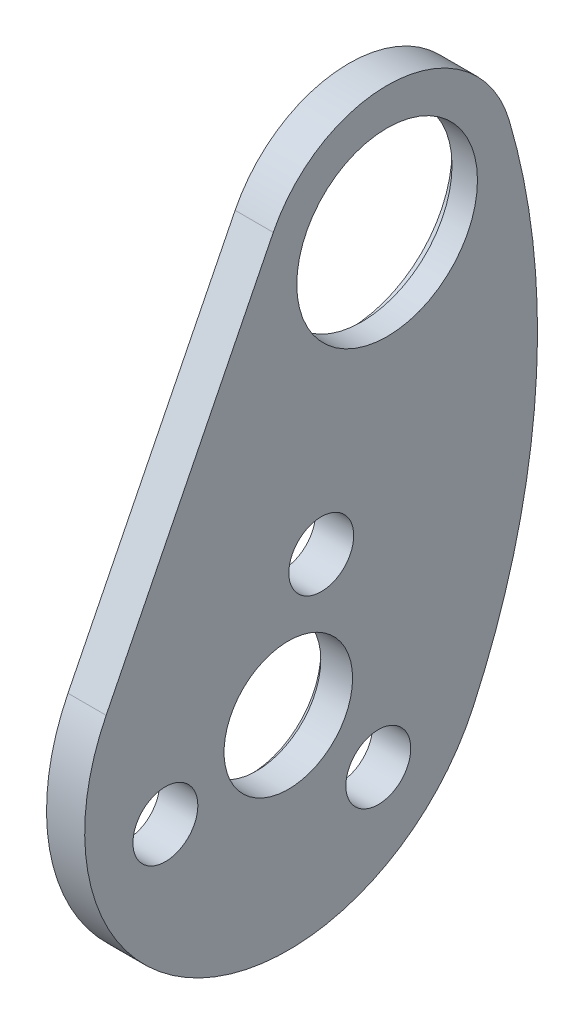
SolidWorks part; units mm, degrees
material "Thornel Mat VMA"
ref_plane "前视基准面" through (0, 0, 0) normal (0, 0, 1) x (1, 0, 0)
ref_plane "上视基准面" through (0, 0, 0) normal (0, 1, 0) x (1, 0, 0)
ref_plane "右视基准面" through (0, 0, 0) normal (1, 0, 0) x (0, 0, -1)
sketch "草图1" plane through (0, 0, 0) normal (1, 0, 0) x (0, 0, -1)
  line L0 (0, 0) -> (-7.7646, -28.9778) construction
  line L1 (-8.9465, 4.4678) -> (-22.0789, -21.8294)
  line L2 (-7.7646, -28.9778) -> (-17.2624, -28.9778) construction
  circle A0 centre (0, 0) radius 10
  circle A1 centre (-7.7646, -28.9778) radius 16
  arc A2 (6.7665, -35.6746) -> (9.5965, 2.8121) centre (-43.1841, -12.6543) ccw
  dimension "D1" = 32
  dimension "D2" = 20
  dimension "D4" = 55
  dimension "D3" = 30
  dimension "D5" = 105
extrude "凸台-拉伸1" add sketch "草图1" along normal blind 3
sketch "草图2" plane through (0, 0, 0) normal (-1, 0, 0) x (0, 0, 1)
  circle A0 centre (0, 0) radius 7.1
  arc A1 (8.9465, 4.4678) -> (-9.5965, 2.8121) centre (0, 0) ccw construction
  circle A2 centre (7.7646, -28.9778) radius 5.05
  arc A3 (-6.7665, -35.6746) -> (22.0789, -21.8294) centre (7.7646, -28.9778) ccw construction
  dimension "D1" = 14.2
  dimension "D2" = 10.1
extrude "切除-拉伸1" cut sketch "草图2" against normal blind 10
sketch "草图3" plane through (0, 0, 0) normal (-1, 0, 0) x (0, 0, 1)
  line L0 (5.1764, -19.3185) -> (7.7646, -28.9778) construction
  line L1 (7.7646, -28.9778) -> (7.7646, -5.7431) construction
  line L2 (7.7646, -28.9778) -> (-20.1149, -28.9778) construction
  circle A0 centre (5.1764, -19.3185) radius 2.55
  circle A1 centre (7.7646, -28.9778) radius 5.05 construction
  dimension "D1" = 5.1
  dimension "D2" = 10
  dimension "D3" = 15
extrude "切除-拉伸2" cut sketch "草图3" against normal blind 10
pattern_circular "阵列(圆周)1" count 3 over 360 about axis through (0, -28.9778, 7.7646) along (1, 0, 0) of "切除-拉伸2"
chamfer "倒角1" distance 0.5 angle 45 1 edges at (0, -28.9778, 12.8146)
sketch "草图4" plane through (0, 0, 0) normal (-1, 0, 0) x (0, 0, 1)
  circle A0 centre (0, 0) radius 8.1
  circle A1 centre (0, 0) radius 7.1 construction
  dimension "D1" = 16.2
extrude "切除-拉伸3" cut sketch "草图4" against normal blind 1
